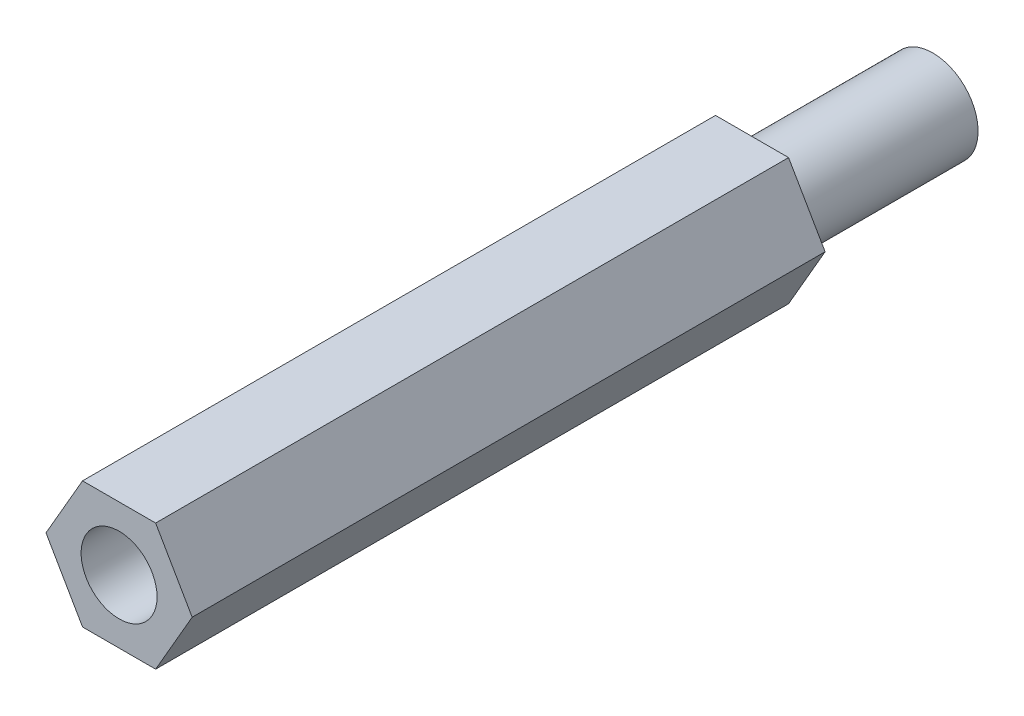
SolidWorks part; units mm, degrees
material "黃銅"
ref_plane "前基準面" through (0, 0, 0) normal (0, 0, 1) x (1, 0, 0)
ref_plane "上基準面" through (0, 0, 0) normal (0, 1, 0) x (1, 0, 0)
ref_plane "右基準面" through (0, 0, 0) normal (1, 0, 0) x (0, 0, -1)
sketch "草圖1" plane through (0, 0, 0) normal (0, 0, 1) x (1, 0, 0)
  line L1 (-2.0207, 3.5) -> (-4.0415, 0)
  line L2 (-4.0415, 0) -> (-2.0207, -3.5)
  line L3 (-2.0207, -3.5) -> (2.0207, -3.5)
  line L4 (2.0207, -3.5) -> (4.0415, 0)
  line L5 (4.0415, 0) -> (2.0207, 3.5)
  line L6 (2.0207, 3.5) -> (-2.0207, 3.5)
  circle A0 centre (0, 0) radius 3.5 construction
  dimension "D1" = 7
extrude "填料-伸長1" add sketch "草圖1" along normal blind 35
sketch "草圖4" plane through (0, 0, 0) normal (0, 0, -1) x (-1, 0, 0)
  circle A0 centre (0, 0) radius 2.5
  dimension "D1" = 5
extrude "填料-伸長2" add sketch "草圖4" along normal blind 10
hole_wizard "M5x0.8 Tapped Hole1" positions "草圖2" profile "草圖3" tap size "M5x0.8" standard "ANSI Metric"
sketch "草圖2" plane through (0, 0, 35) normal (0, 0, 1) x (1, 0, 0)
  point P0 (0, 0)
sketch "草圖3" plane through (0, 0, 35) normal (1, 0, 0) x (0, -1, 0)
  line L0 (0, 0) -> (0, 15.2618)
  line L1 (0, 15.2618) -> (2.1, 14)
  line L2 (2.1, 14) -> (2.1, 0)
  line L5 (2.1, 0) -> (0, 0)
  line L10 (0, 15.2618) -> (-2.1, 14) construction
  line L11 (0, -6.35) -> (0, 107.95) construction
  dimension "螺孔鑽直徑" = 4.2
  dimension "螺孔鑽深度" = 14
  dimension "導頭角度" = 118
